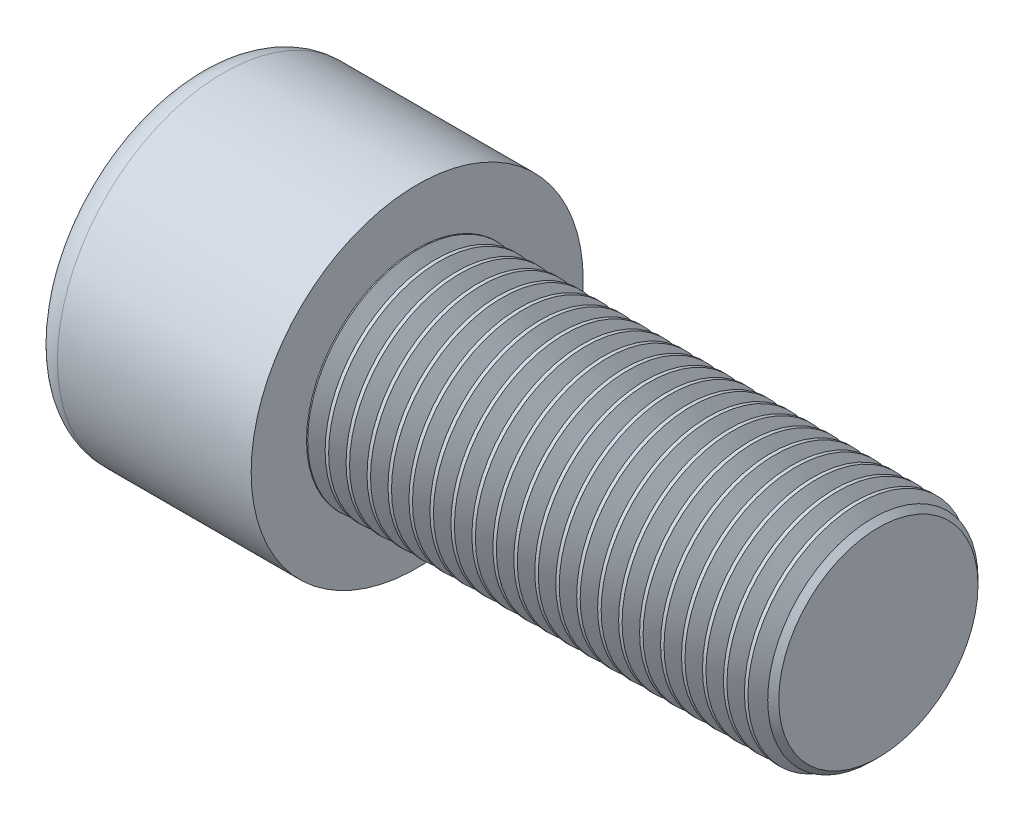
SolidWorks part; units mm, degrees
ref_plane "Front" through (0, 0, 0) normal (0, 0, 1) x (1, 0, 0)
ref_plane "Top" through (0, 0, 0) normal (0, 1, 0) x (1, 0, 0)
ref_plane "Right" through (0, 0, 0) normal (1, 0, 0) x (0, 0, -1)
sketch "Sketch1" plane through (0, 0, 0) normal (1, 0, 0) x (0, 0, -1)
  circle A0 centre (0, 0) radius 9
  dimension "dk" = 18
extrude "BaseHead" add sketch "Sketch1" along normal blind 12
sketch "Sketch2" plane through (12, 0, 0) normal (1, 0, 0) x (0, 0, -1)
  circle A0 centre (0, 0) radius 6
  dimension "d" = 12
extrude "BaseBody" add sketch "Sketch2" along normal blind 25
cosmetic thread "ThreadCosmetic1" [suppressed] parameters "b"=25, "D2"=10.106
sketch "Sketch3" plane through (0, 0, 0) normal (1, 0, 0) x (0, 0, -1)
  line L1 (5.7735, 0) -> (2.8868, 5)
  line L2 (2.8868, 5) -> (-2.8868, 5)
  line L3 (-2.8868, 5) -> (-5.7735, 0)
  line L4 (-5.7735, 0) -> (-2.8868, -5)
  line L5 (-2.8868, -5) -> (2.8868, -5)
  line L6 (2.8868, -5) -> (5.7735, 0)
  circle A0 centre (0, 0) radius 5 construction
  dimension "s" = 10
  dimension "e" = 11.547
extrude "HexagonSocket" cut sketch "Sketch3" along normal blind 6
sketch "Sketch4" plane through (-4.1961, 0.75, 0) normal (0, 0, 1) x (-1, 0, 0)
  line L0 (-10.1961, 5.75) -> (-13.0829, 0.75)
  line L2 (-13.0829, 0.75) -> (-10.1961, 0.75)
  line L3 (-10.1961, 0.75) -> (-10.1961, 5.75)
  line L4 (-5.0351, 0.75) -> (0.839, 0.75) construction
  line L5 (-41.1961, 0.75) -> (-16.1961, 0.75) construction
  line L6 (-16.1961, 0.75) -> (-4.1961, 0.75) construction
  dimension "m" = 60
revolve "Cut-Revolve1" cut sketch "Sketch4" angle 360 about L4
fillet "HeadFillet" [suppressed] radius 0.6
fillet "TopFillet" radius 1.5 1 edges at (0, 0, -9)
chamfer "Chamfer1" distance 0.6 angle 45 1 edges at (37, 0, -6)
sketch "Sketch5" plane through (0, 0, 0) normal (0, 0, 1) x (1, 0, 0)
  line L0 (36.4, 5.1799) -> (36.8735, 6)
  line L1 (36.8735, 6) -> (36.8735, 6.947)
  line L2 (36.8735, 6.947) -> (35.9265, 6.947)
  line L3 (35.9265, 6.947) -> (35.9265, 6)
  line L4 (35.9265, 6) -> (36.4, 5.1799)
  line L5 (0, 0) -> (7.8886, 0) construction
  line L6 (36.4, -6) -> (36.4, 6) construction
  dimension "D1" = 12
  dimension "D2" = 0.947
revolve "Cut-Revolve10" cut sketch "Sketch5" angle 360 about L5
pattern_linear "LPattern10" count 22 spacing 1.1364 along (-1, 0, 0) of "Cut-Revolve10"
equation "\"r1@TopFillet\" = \"d@Sketch2\" / 8"
equation "\"D1@Chamfer1\" = \"r@HeadFillet\""
equation "\"D1@Sketch5\" = \"d@Sketch2\""
equation "\"D2@Sketch5\" =  ( \"d@Sketch2\" - \"D2@ThreadCosmetic1\" )  / 2"
equation "\"D3@LPattern10\" = \"D2@Sketch5\" * 1.2"
equation "\"D1@LPattern10\" = \"b@ThreadCosmetic1\" / \"D3@LPattern10\""
